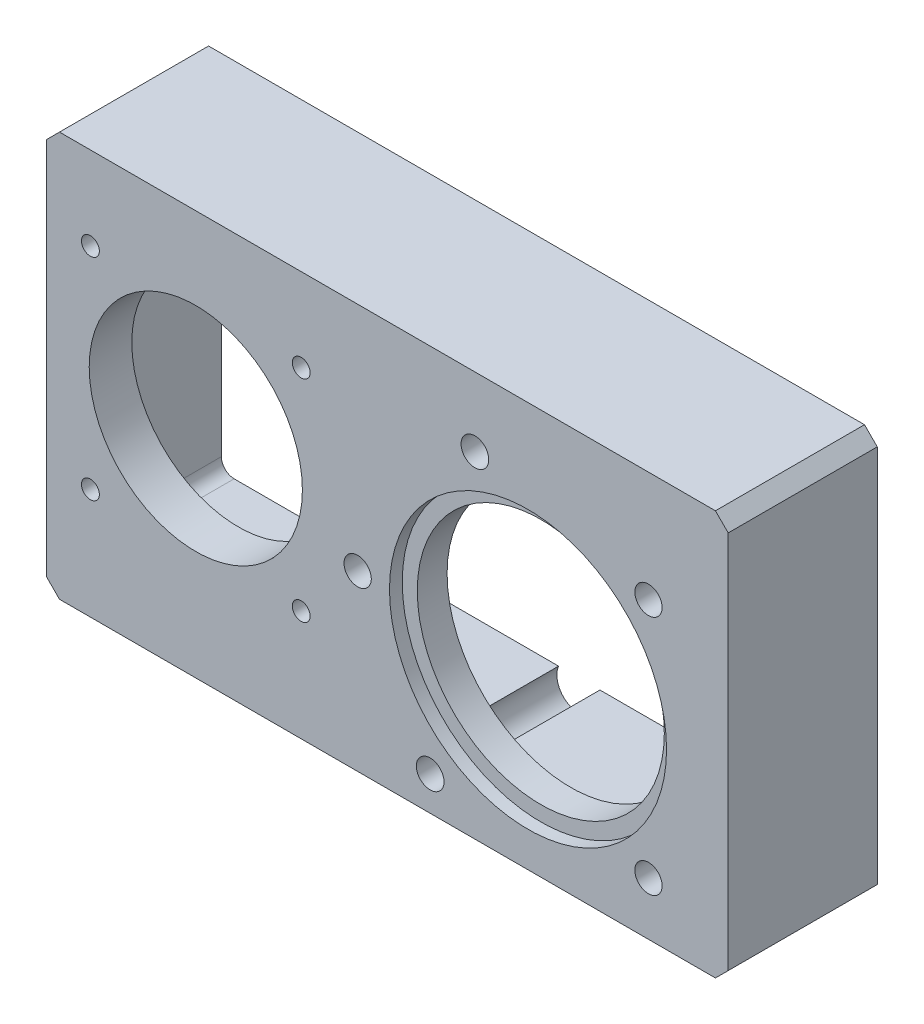
SolidWorks part; units mm, degrees
ref_plane "前视基准面" through (0, 0, 0) normal (0, 0, 1) x (1, 0, 0)
ref_plane "上视基准面" through (0, 0, 0) normal (0, 1, 0) x (1, 0, 0)
ref_plane "右视基准面" through (0, 0, 0) normal (1, 0, 0) x (0, 0, -1)
other "Configuration Table"
sketch "草图1" plane through (0, 0, 0) normal (0, 0, 1) x (1, 0, 0)
  line L2 (0, 0) -> (0, -60)
  line L5 (160, -60) -> (160, 35)
  line L6 (160, 35) -> (68, 35)
  line L8 (68, 35) -> (0, 35)
  line L9 (0, 35) -> (0, 0)
  line L10 (160, -60) -> (0, -60)
  dimension "D1" = 160
  dimension "D4" = 95
extrude "凸台-拉伸1" add sketch "草图1" along normal blind 35
sketch "草图4" plane through (0, 0, 0) normal (0, 0, -1) x (-1, 0, 0)
  line L0 (0, 35) -> (0, -60) construction
  line L1 (-6, -50) -> (-148, -50)
  line L2 (-6, -50) -> (-6, 25)
  line L3 (-6, 25) -> (-148, 25)
  line L4 (-148, -50) -> (-148, 25)
  line L5 (-160, 35) -> (0, 35) construction
  circle A0 centre (-113, -19.25) radius 27.5 construction
  dimension "D1" = 55
  dimension "D2" = 75
  dimension "D3" = 142
  dimension "D4" = 6
  dimension "D5" = 10
extrude "切除-拉伸2" cut sketch "草图4" against normal blind 25
sketch "草图5" plane through (0, 0, 25) normal (0, 0, -1) x (-1, 0, 0)
  circle A0 centre (-113, -19.25) radius 29
  dimension "D1" = 58
extrude "切除-拉伸3" cut sketch "草图5" against normal through all
chamfer "倒角3" distance 3 angle 45 4 edges at (160, -60, 17.5) (160, 35, 17.5) (0, -60, 17.5) (0, 35, 17.5)
fillet "圆角2" radius 3 4 edges at (148, 25, 12.5) (148, -50, 12.5) (6, 25, 12.5) (6, -50, 12.5)
sketch "草图7" plane through (0, 0, 25) normal (0, 0, -1) x (-1, 0, 0)
  circle A2 centre (-73, -19.25) radius 3.2
  circle A3 centre (-73, -19.25) radius 3.2
  circle A5 centre (-141.2843, -47.5343) radius 3.2
  circle A6 centre (-141.2843, -47.5343) radius 3.2
  circle A8 centre (-141.2843, 9.0343) radius 3.2
  circle A9 centre (-141.2843, 9.0343) radius 3.2
  circle A18 centre (-113, -19.25) radius 40 construction
  circle A19 centre (-100.5345, 18.758) radius 3.25
  circle A23 centre (-90.0258, -51.9943) radius 3.25
  dimension "D4" = 80
  dimension "D5" = 6.5
  dimension "D7" = 6.5
  dimension "D1" = 0.6
  dimension "D2" = 0.6
  dimension "D3" = 0.6
extrude "切除-拉伸4" cut sketch "草图7" against normal through all
sketch "草图8" plane through (0, 0, 25) normal (0, 0, -1) x (-1, 0, 0)
  circle A0 centre (-35, -9.275) radius 25.025
  dimension "D1" = 50.05
extrude "切除-拉伸5" cut sketch "草图8" against normal through all
sketch "草图9" plane through (0, 0, 0) normal (0, 0, -1) x (-1, 0, 0)
  circle A0 centre (-141.2843, -47.5343) radius 5.25
  circle A1 centre (-90.0258, -51.9943) radius 5.25
  dimension "D1" = 10.5
  dimension "D2" = 10.5
extrude "切除-拉伸6" cut sketch "草图9" against normal up to surface (25 mm away) up to face at (9.975, -9.275, 25)
hole_wizard "M6 螺纹孔1" positions "草图10" profile "草图11" tap size "M6" standard "GB"
sketch "草图10" plane through (0, 0, 0) normal (0, 0, -1) x (-1, 0, 0)
  point P0 (-154, 29)
  point P3 (-80, 29)
  point P6 (-6, 29)
  point P12 (-154, -54)
  point P14 (-6, -54)
  point P19 (-65, -54)
sketch "草图11" plane through (154, 29, 0) normal (1, 0, 0) x (0, 1, 0)
  line L0 (0, 0) -> (0, 16.5022)
  line L1 (0, 16.5022) -> (2.5, 15)
  line L2 (2.5, 15) -> (2.5, 0)
  line L5 (2.5, 0) -> (0, 0)
  line L10 (0, 16.5022) -> (-2.5, 15) construction
  line L11 (0, -6.35) -> (0, 107.95) construction
  dimension "螺纹孔钻头直径" = 5
  dimension "螺纹孔钻头深度" = 15
  dimension "导头角度" = 118
cosmetic thread "孔螺蚊线1" parameters "D1"=12, "D2"=6
cosmetic thread "孔螺蚊线2" parameters "D1"=12, "D2"=6
cosmetic thread "孔螺蚊线3" parameters "D1"=12, "D2"=6
cosmetic thread "孔螺蚊线4" parameters "D1"=12, "D2"=6
cosmetic thread "孔螺蚊线5" parameters "D1"=12, "D2"=6
cosmetic thread "孔螺蚊线6" parameters "D1"=12, "D2"=6
sketch "草图14" plane through (0, 0, 35) normal (0, 0, 1) x (1, 0, 0)
  circle A0 centre (10.2513, 15.4737) radius 2.75
  arc A1 (59.7487, 12.7237) -> (59.7487, 18.2237) centre (59.7487, 15.4737) ccw construction
  arc A2 (59.7487, 12.7237) -> (59.7487, 18.2237) centre (59.7487, 15.4737) ccw
  arc A3 (59.7487, 18.2237) -> (59.7487, 12.7237) centre (59.7487, 15.4737) ccw construction
  arc A4 (59.7487, 18.2237) -> (59.7487, 12.7237) centre (59.7487, 15.4737) ccw
  arc A5 (10.2513, -31.2737) -> (10.2513, -36.7737) centre (10.2513, -34.0237) ccw construction
  arc A6 (10.2513, -31.2737) -> (10.2513, -36.7737) centre (10.2513, -34.0237) ccw
  arc A7 (10.2513, -36.7737) -> (10.2513, -31.2737) centre (10.2513, -34.0237) ccw construction
  arc A8 (10.2513, -36.7737) -> (10.2513, -31.2737) centre (10.2513, -34.0237) ccw
  arc A9 (59.7487, -31.2737) -> (59.7487, -36.7737) centre (59.7487, -34.0237) ccw construction
  arc A10 (59.7487, -31.2737) -> (59.7487, -36.7737) centre (59.7487, -34.0237) ccw
  arc A11 (59.7487, -36.7737) -> (59.7487, -31.2737) centre (59.7487, -34.0237) ccw construction
  arc A12 (59.7487, -36.7737) -> (59.7487, -31.2737) centre (59.7487, -34.0237) ccw
hole_wizard "M5 螺纹孔1" positions "草图15" profile "草图16" tap size "M5" standard "GB" end condition through all
sketch "草图15" plane through (0, 0, 35) normal (0, 0, 1) x (1, 0, 0)
  point P0 (10.2513, 15.4737)
  point P3 (59.7487, 15.4737)
  point P6 (59.7487, -34.0237)
  point P9 (10.2513, -34.0237)
sketch "草图16" plane through (10.2513, 15.4737, 35) normal (1, 0, 0) x (0, -1, 0)
  line L0 (0, 0) -> (0, 35)
  line L1 (0, 35) -> (2.1, 35)
  line L2 (2.1, 35) -> (2.1, 0)
  line L5 (2.1, 0) -> (0, 0)
  line L11 (0, -6.35) -> (0, 107.95) construction
  dimension "通孔螺纹孔钻头直径" = 4.2
  dimension "通孔螺纹孔钻头深度" = 35
cosmetic thread "孔螺蚊线7" parameters "D2"=5
cosmetic thread "孔螺蚊线8" parameters "D2"=5
cosmetic thread "孔螺蚊线9" parameters "D2"=5
cosmetic thread "孔螺蚊线10" parameters "D2"=5
sketch "草图17" plane through (0, 0, 35) normal (0, 0, 1) x (1, 0, 0)
  circle A0 centre (113, -19.25) radius 32.525
  dimension "D1" = 65.05
extrude "切除-拉伸7" cut sketch "草图17" against normal blind 3
